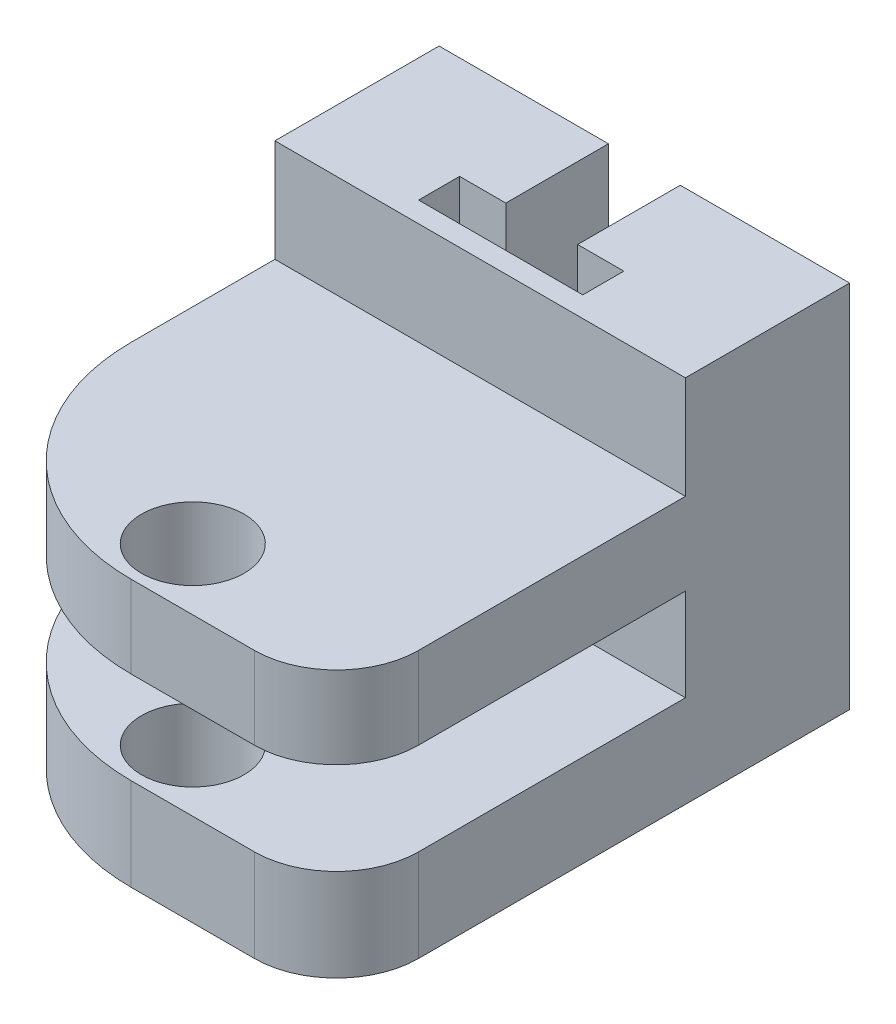
SolidWorks part; units mm, degrees
ref_plane "Front Plane" through (0, 0, 0) normal (0, 0, 1) x (1, 0, 0)
ref_plane "Top Plane" through (0, 0, 0) normal (0, 1, 0) x (1, 0, 0)
ref_plane "Right Plane" through (0, 0, 0) normal (1, 0, 0) x (0, 0, -1)
sketch "Croquis1" plane through (0, 0, 0) normal (0, 1, 0) x (1, 0, 0)
  line L0 (-1.5029, 4.4252) -> (-1.5029, -0.5748)
  line L1 (-1.5029, -0.5748) -> (-3.7529, -0.5748)
  line L2 (-3.7529, -0.5748) -> (-3.7529, -2.5748)
  line L3 (-3.7529, -2.5748) -> (4.2471, -2.5748)
  line L4 (4.2471, -2.5748) -> (4.2471, -0.5748)
  line L5 (4.2471, -0.5748) -> (1.9971, -0.5748)
  line L6 (1.9971, -0.5748) -> (1.9971, 4.4252)
  line L7 (1.9971, 4.4252) -> (10.2471, 4.4252)
  line L8 (10.2471, 4.4252) -> (10.2471, -9.3828)
  line L10 (-9.7529, -10.5748) -> (-9.7529, 4.4252)
  line L11 (-9.7529, 4.4252) -> (-1.5029, 4.4252)
  line L12 (0.2471, -20.5748) -> (10.2471, -20.5748)
  line L13 (10.2471, -20.5748) -> (10.2471, -9.3828)
  circle A0 centre (0.2471, -17.5748) radius 2.5
  arc A2 (-9.7529, -10.5748) -> (0.2471, -20.5748) centre (0.2471, -10.5748) ccw
  point P17 (0, 0)
  point P19 (0, 0)
  point P20 (0.2471, -2.5748)
  point P21 (0, 0)
  point P22 (-5.4092, -12.7325)
  point P23 (0, 0)
  dimension "D7" = 5
  dimension "D9" = 3
  dimension "D1" = 3.5
  dimension "D2" = 2
  dimension "D3" = 5
  dimension "D4" = 6
  dimension "D5" = 6
  dimension "D6" = 8
  dimension "D8" = 15
extrude "Saliente-Extruir1" add sketch "Croquis1" along normal blind 3
fillet "Redondeo1" radius 4 1 edges at (10.2471, 1.5, 20.5748)
sketch "Croquis2" plane through (0, 3, 0) normal (0, 1, 0) x (1, 0, 0)
  line L0 (-9.7529, -3.5748) -> (10.2471, -3.5748)
  line L1 (-9.7529, 4.4252) -> (-9.7529, -10.5748) construction
  line L2 (10.2471, -16.5748) -> (10.2471, 4.4252) construction
  line L3 (10.2471, -3.5748) -> (10.2471, 4.4252)
  line L4 (10.2471, 4.4252) -> (1.9971, 4.4252)
  line L5 (1.9971, 4.4252) -> (1.9971, -0.5748)
  line L6 (1.9971, -0.5748) -> (4.2471, -0.5748)
  line L7 (4.2471, -0.5748) -> (4.2471, -2.5748)
  line L8 (4.2471, -2.5748) -> (-3.7529, -2.5748)
  line L9 (-3.7529, -2.5748) -> (-3.7529, -0.5748)
  line L10 (-3.7529, -0.5748) -> (-1.5029, -0.5748)
  line L11 (-1.5029, -0.5748) -> (-1.5029, 4.4252)
  line L12 (-1.5029, 4.4252) -> (-9.7529, 4.4252)
  line L13 (-9.7529, 4.4252) -> (-9.7529, -3.5748)
  circle A0 centre (0.2471, -17.5748) radius 2.5 construction
  dimension "D1" = 14
extrude "Saliente-Extruir2" add sketch "Croquis2" along normal blind 15
sketch "Croquis3" plane through (0, 0, 0) normal (0, -1, 0) x (1, 0, 0)
  line L0 (10.2471, -4.4252) -> (1.9971, -4.4252) construction
  line L1 (-4.3524, 3.0287) -> (4.7573, 3.0287)
  line L2 (-4.3524, 3.0287) -> (-4.3524, -4.4252)
  line L3 (-4.3524, -4.4252) -> (4.7573, -4.4252)
  line L4 (4.7573, 3.0287) -> (4.7573, -4.4252)
extrude "Saliente-Extruir3" add sketch "Croquis3" against normal blind 4 contours L3 L4 L1 L2
sketch "Croquis4" plane through (0, 0, 0) normal (0, -1, 0) x (1, 0, 0)
  line L0 (-9.7529, -4.4252) -> (10.2471, -4.4252)
  line L1 (10.2471, -4.4252) -> (10.2471, 16.5748)
  line L2 (-9.7529, -4.4252) -> (-9.7529, 10.5748)
  line L3 (0.2471, 20.5748) -> (6.2471, 20.5748)
  arc A1 (10.2471, 16.5748) -> (6.2471, 20.5748) centre (6.2471, 16.5748) ccw
  arc A4 (0.2471, 20.5748) -> (-9.7529, 10.5748) centre (0.2471, 10.5748) ccw
  circle A5 centre (0.2471, 17.5748) radius 2.5
  circle A6 centre (0.2471, 17.5748) radius 2.5 construction
extrude "Saliente-Extruir4" add sketch "Croquis4" against normal blind 13
sketch "Croquis5" plane through (0, 0, 20.5748) normal (0, 0, 1) x (1, 0, 0)
  line L0 (-9.7529, 13) -> (-9.7529, 0) construction
  line L1 (-9.7529, 9) -> (10.2471, 9)
  line L2 (-9.7529, 9) -> (-9.7529, 4.5)
  line L3 (-9.7529, 4.5) -> (10.2471, 4.5)
  line L4 (10.2471, 9) -> (10.2471, 4.5)
  line L5 (10.2471, 13) -> (10.2471, 0) construction
  line L6 (6.2471, 13) -> (0.2471, 13) construction
  dimension "D1" = 4
  dimension "D2" = 4.5
extrude "Cortar-Extruir1" cut sketch "Croquis5" against normal up to surface (17 mm away) contours L1 L4 L3 L2 up to face at (0.2471, 15.5, 3.5748)
sketch "Croquis6" plane through (0, 13, 0) normal (0, 1, 0) x (1, 0, 0)
  line L0 (-1.5029, 4.4252) -> (-1.5029, -0.5748)
  line L1 (-1.5029, -0.5748) -> (-3.7529, -0.5748)
  line L2 (-3.7529, -0.5748) -> (-3.7529, -2.5748)
  line L3 (-3.7529, -2.5748) -> (4.2471, -2.5748)
  line L4 (4.2471, -2.5748) -> (4.2471, -0.5748)
  line L5 (4.2471, -0.5748) -> (1.9971, -0.5748)
  line L6 (1.9971, -0.5748) -> (1.9971, 4.4252)
  line L7 (1.9971, 4.4252) -> (-1.5029, 4.4252)
extrude "Cortar-Extruir2" cut sketch "Croquis6" against normal blind 6.5
